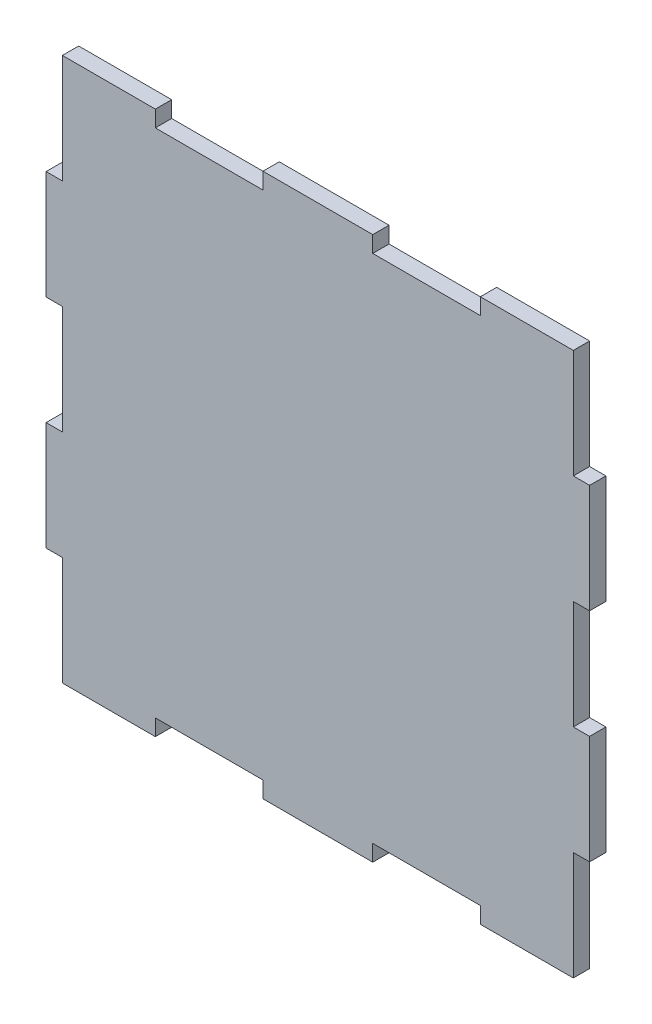
SolidWorks part; units mm, degrees
ref_plane "Front Plane" through (0, 0, 0) normal (0, 0, 1) x (1, 0, 0)
ref_plane "Top Plane" through (0, 0, 0) normal (0, 1, 0) x (1, 0, 0)
ref_plane "Right Plane" through (0, 0, 0) normal (1, 0, 0) x (0, 0, -1)
sketch "Sketch1" plane through (0, 0, 0) normal (0, 0, 1) x (1, 0, 0)
  line L0 (60.1, 100) -> (60.1, 97)
  line L1 (0, 0) -> (100, 0)
  line L2 (0, 0) -> (0, 100)
  line L3 (0, 100) -> (100, 100)
  line L4 (100, 0) -> (100, 100)
  line L5 (20.1, 100) -> (39.9, 100)
  line L6 (20.1, 100) -> (20.1, 97)
  line L7 (20.1, 97) -> (39.9, 97)
  line L8 (39.9, 100) -> (39.9, 97)
  line L9 (60.1, 100) -> (79.9, 100)
  line L10 (79.9, 100) -> (79.9, 97)
  line L11 (60.1, 97) -> (79.9, 97)
  line L12 (3, 60) -> (3, 40)
  line L13 (3, 100) -> (0, 100)
  line L14 (3, 100) -> (3, 80)
  line L15 (3, 80) -> (0, 80)
  line L16 (0, 100) -> (0, 80)
  line L17 (3, 60) -> (0, 60)
  line L18 (0, 60) -> (0, 40)
  line L19 (3, 40) -> (0, 40)
  line L20 (3, 20) -> (3, 0)
  line L21 (3, 20) -> (0, 20)
  line L22 (0, 20) -> (0, 0)
  line L23 (3, 0) -> (0, 0)
  line L24 (-900, 50) -> (49100, 50) construction
  line L25 (50, -900) -> (50, 49100) construction
  line L26 (60.1, 0) -> (79.9, 0)
  line L27 (79.9, 0) -> (79.9, 3)
  line L28 (60.1, 3) -> (79.9, 3)
  line L29 (60.1, 0) -> (60.1, 3)
  line L30 (20.1, 3) -> (39.9, 3)
  line L31 (39.9, 0) -> (39.9, 3)
  line L32 (20.1, 0) -> (39.9, 0)
  line L33 (20.1, 0) -> (20.1, 3)
  line L34 (97, 20) -> (100, 20)
  line L35 (100, 20) -> (100, 0)
  line L36 (97, 0) -> (100, 0)
  line L37 (97, 20) -> (97, 0)
  line L38 (97, 60) -> (100, 60)
  line L39 (100, 60) -> (100, 40)
  line L40 (97, 40) -> (100, 40)
  line L41 (97, 60) -> (97, 40)
  line L42 (97, 80) -> (100, 80)
  line L43 (100, 100) -> (100, 80)
  line L44 (97, 100) -> (100, 100)
  line L45 (97, 100) -> (97, 80)
  point P27 (100, 50)
  point P30 (50, 100)
  dimension "D1" = 100
  dimension "D2" = 100
  dimension "D3" = 19.8
  dimension "D4" = 3
  dimension "D5" = 20.1
  dimension "D7" = 20.1
  dimension "D8" = 3
  dimension "D9" = 20
  dimension "D6" = 2
  dimension "D10" = 3
extrude "Boss-Extrude1" add sketch "Sketch1" along normal blind 3 contours L45 L3 L10 L11 L0 L8 L7 L6 L14 L15 L2 L17 L12 L19 L21 L20 L1 L33 L30 L31 L29 L28 L27 L37 L34 L4 L40 L41 L38 L42
